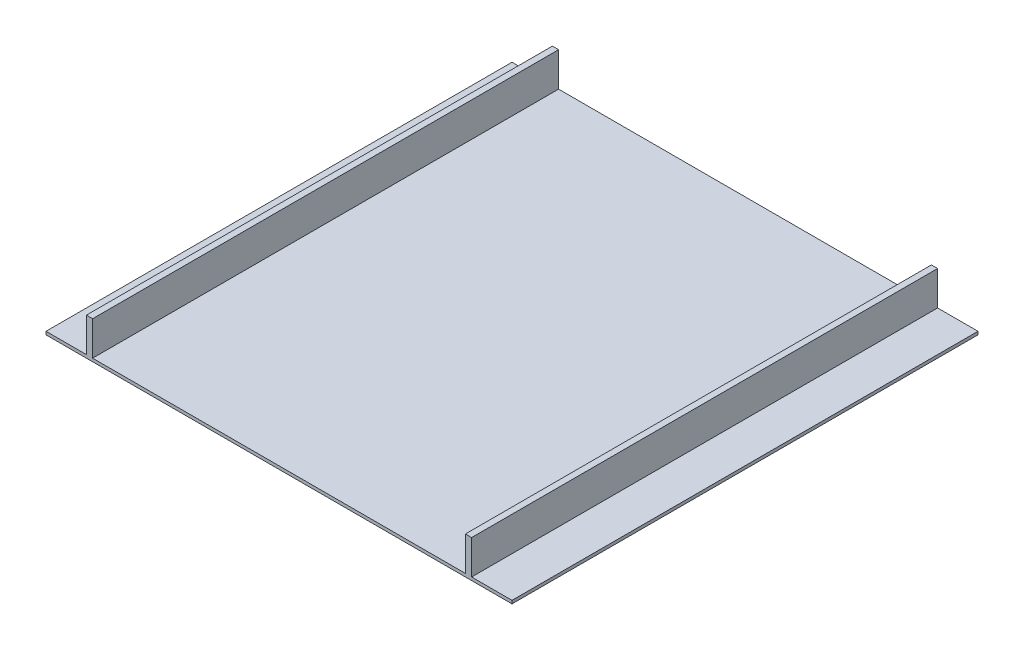
SolidWorks part; units mm, degrees
ref_plane "Front Plane" through (0, 0, 0) normal (0, 0, 1) x (1, 0, 0)
ref_plane "Top Plane" through (0, 0, 0) normal (0, 1, 0) x (1, 0, 0)
ref_plane "Right Plane" through (0, 0, 0) normal (1, 0, 0) x (0, 0, -1)
sketch "Sketch2" plane through (0, 0, 0) normal (0, 1, 0) x (1, 0, 0)
  line L1 (-750, 750) -> (750, 750)
  line L2 (-750, 750) -> (-750, -750)
  line L3 (-750, -750) -> (750, -750)
  line L4 (750, 750) -> (750, -750)
  line L5 (-750, 750) -> (750, -750) construction
  line L6 (-750, -750) -> (750, 750) construction
  point P0 (0, 0)
  dimension "D1" = 1500
  dimension "D2" = 1500
extrude "Boss-Extrude1" add sketch "Sketch2" along normal blind 10
sketch "Sketch3" plane through (0, 10, 0) normal (0, 1, 0) x (1, 0, 0)
  line L0 (620, 750) -> (620, -750) construction
  line L1 (750, 750) -> (-750, 750) construction
  line L2 (-750, -750) -> (750, -750) construction
  line L3 (600, 750) -> (600, -750) construction
  line L4 (750, -750) -> (750, 750) construction
  line L5 (-750, -600) -> (750, -600) construction
  line L6 (-750, 750) -> (-750, -750) construction
  line L7 (-750, -620) -> (750, -620) construction
  line L8 (-750, 0) -> (750, 0) construction
  line L9 (0, 750) -> (0, -750) construction
  line L10 (-750, 620) -> (750, 620) construction
  line L11 (-750, 600) -> (750, 600) construction
  line L12 (-620, 750) -> (-620, -750) construction
  line L13 (-600, 750) -> (-600, -750) construction
  line L15 (-620, 750) -> (-600, 750)
  line L16 (-620, 750) -> (-620, -750)
  line L17 (-620, -750) -> (-600, -750)
  line L18 (-600, 750) -> (-600, -750)
  line L19 (600, 750) -> (620, 750)
  line L20 (600, 750) -> (600, -750)
  line L21 (600, -750) -> (620, -750)
  line L22 (620, 750) -> (620, -750)
  dimension "D6" = 150
  dimension "D5" = 20
  dimension "D7" = 20
  dimension "D8" = 150
extrude "Boss-Extrude2" add sketch "Sketch3" along normal blind 110
equation "\"CellSize\"=1500"
equation "\"D1@Sketch2\"=\"CellSize\""
equation "\"D2@Sketch2\"=\"CellSize\""
equation "\"TrackWidth\"= 1200"
equation "\"C\"=342.079"
equation "\"WallWidth\"=20"
equation "\"D6@Sketch3\"=\"EdgeWidth\""
equation "\"D5@Sketch3\"=\"WallWidth\""
equation "\"D7@Sketch3\"=\"WallWidth\""
equation "\"EdgeWidth\"= ( \"CellSize\" - \"TrackWidth\" ) / 2"
equation "\"D8@Sketch3\"=\"EdgeWidth\""
